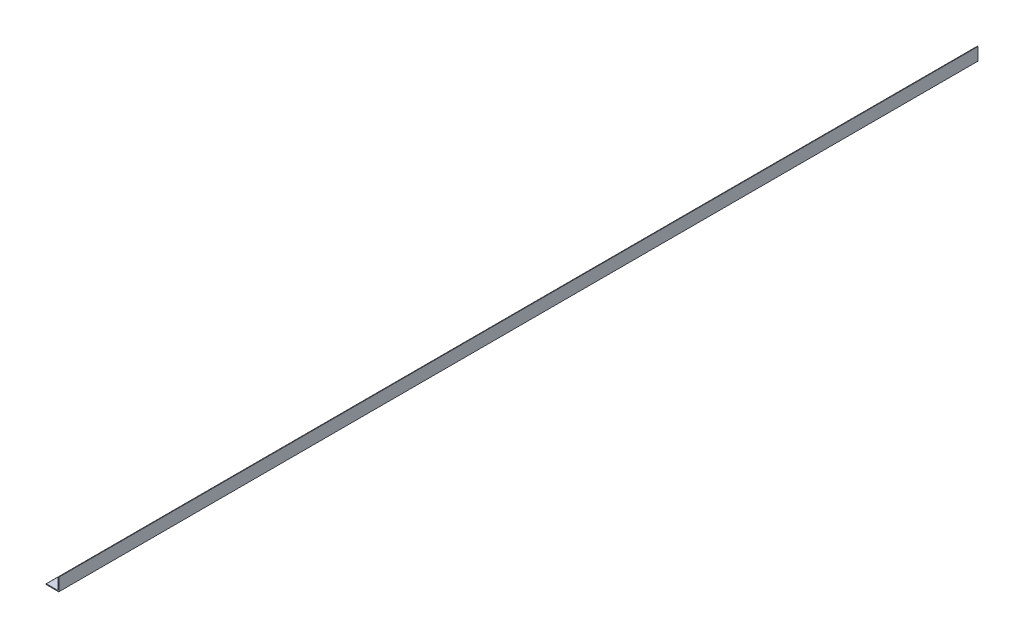
SolidWorks part; units mm, degrees
ref_plane "Front Plane" through (0, 0, 0) normal (0, 0, 1) x (1, 0, 0)
ref_plane "Top Plane" through (0, 0, 0) normal (0, 1, 0) x (1, 0, 0)
ref_plane "Right Plane" through (0, 0, 0) normal (1, 0, 0) x (0, 0, -1)
sketch "Sketch0" plane through (0, 0, 0) normal (0, 0, 1) x (1, 0, 0)
  line L0 (-12.7, -12.7) -> (12.7, -12.7)
  line L1 (12.7, -12.7) -> (12.7, 12.7)
  line L2 (12.7, 0) -> (0, 0) construction
  line L3 (0, 0) -> (0, -12.7) construction
  line L4 (11.1125, -9.5377) -> (11.1125, 12.7) construction
  line L5 (9.5377, -11.1125) -> (-12.7, -11.1125) construction
  arc A0 (11.1125, -9.5377) -> (9.5377, -11.1125) centre (9.5377, -9.5377) cw
  point P3 (10.6513, -10.6513)
  dimension "Inside Corner Radius" = 1.5748
  dimension "Outside Height" = 25.4
  dimension "Inside Height" = 23.8125
  dimension "Inside Width" = 23.8125
  dimension "Wall Thickness" = 1.5875
  dimension "D1" = 1.5875
  dimension "Outside Width" = 25.4
sketch "Sketch1" plane through (0, 0, 0) normal (1, 0, 0) x (0, 0, -1)
  line L0 (914.4, 0) -> (-914.4, 0)
  point P4 (0, 0)
  dimension "Length" = 1828.8
sketch "Sketch2" plane through (0, 0, 0) normal (0, 0, 1) x (1, 0, 0)
  line L0 (-12.7, -12.7) -> (12.7, -12.7)
  line L1 (12.7, -12.7) -> (12.7, 12.7)
  line L2 (12.7, 12.7) -> (11.1125, 12.7) construction
  line L3 (11.1125, 11.9062) -> (11.1125, -9.5377)
  line L4 (9.5377, -11.1125) -> (-11.9062, -11.1125)
  line L5 (-12.7, -12.7) -> (-12.7, -11.1125) construction
  line L6 (11.9062, 12.7) -> (12.7, 12.7)
  line L7 (-12.7, -11.9062) -> (-12.7, -12.7)
  line L8 (12.7, 0) -> (0, 0) construction
  line L9 (0, 0) -> (0, -12.7) construction
  arc A0 (11.1125, 11.9062) -> (11.9062, 12.7) centre (11.9062, 11.9062) cw
  arc A1 (-12.7, -11.9062) -> (-11.9062, -11.1125) centre (-11.9062, -11.9062) cw
  arc A2 (11.1125, -9.5377) -> (9.5377, -11.1125) centre (9.5377, -9.5377) cw
  dimension "Inside Radius" = 1.5748
  dimension "Height" = 25.4
  dimension "Width" = 25.4
  dimension "Thickness" = 1.5875
extrude "Boss-Extrude1" add sketch "Sketch2" along normal mid plane 1828.8
sketch "Break Locations" plane through (0, 0, 0) normal (1, 0, 0) x (0, 0, -1)
  line L0 (-888.492, 0) -> (888.492, 0)
  line L1 (-914.4, -12.7) -> (-914.4, 12.7) construction
  line L2 (914.4, -12.7) -> (914.4, 12.7) construction
  point P0 (-892.81, 0)
  point P1 (892.81, 0)
  point P10 (0, 0)
  point P11 (888.492, 0)
  point P13 (-888.492, 0)
  dimension "D1" = 21.59
  dimension "D2" = 21.59
  dimension "D3" = 25.908
hole_wizard "1/4-20 Tapped Hole1" positions "Sketch3" profile "Sketch4" tap size "1/4-20" standard "ANSI Inch" end condition through all
sketch "Sketch3" plane through (0, -11.1125, 0) normal (0, 1, 0) x (1, 0, 0)
  line L2 (11.1125, -914.4) -> (11.1125, 914.4) construction
  line L4 (9.5377, 914.4) -> (-11.9062, 914.4) construction
  point P0 (-1.5875, -705.104)
  point P3 (-1.5875, -705.104)
  point P11 (-1.5875, -249.428)
  point P13 (-1.5875, 661.924)
  point P15 (-1.5875, 206.248)
  dimension "D1" = 12.7
  dimension "D2" = 252.476
  dimension "D3" = 455.676
  dimension "D4" = 455.676
  dimension "D5" = 455.676
cosmetic thread "Hole Thread1" parameters "D2"=6.35
sketch "Sketch4" plane through (-1.5875, -11.1125, 705.104) normal (1, 0, 0) x (0, 0, 1)
  line L0 (0, 0) -> (0, 1.5875)
  line L1 (0, 1.5875) -> (2.5527, 1.5875)
  line L2 (2.5527, 1.5875) -> (2.5527, 0)
  line L5 (2.5527, 0) -> (0, 0)
  line L11 (0, -6.35) -> (0, 107.95) construction
  dimension "Thru Tap Drill Dia." = 5.1054
  dimension "Thru Tap Drill Depth" = 1.5875
cosmetic thread "Hole Thread2" parameters "D2"=6.35
cosmetic thread "Hole Thread3" parameters "D2"=6.35
cosmetic thread "Hole Thread4" parameters "D2"=6.35
sketch "Sketch5" plane through (0, -11.1125, 0) normal (0, 1, 0) x (1, 0, 0)
  line L0 (-1.5875, 701.675) -> (-1.5875, 720.725) construction
  line L1 (-4.6355, 701.675) -> (-4.6355, 720.725)
  line L2 (1.4605, 701.675) -> (1.4605, 720.725)
  line L3 (9.5377, 914.4) -> (-11.9062, 914.4) construction
  line L4 (11.1125, -914.4) -> (11.1125, 914.4) construction
  line L5 (-1.5875, 304.8) -> (-1.5875, 285.75) construction
  line L6 (1.4605, 304.8) -> (1.4605, 285.75)
  line L7 (-4.6355, 304.8) -> (-4.6355, 285.75)
  line L8 (-321.8956, 0) -> (278.4939, 0) construction
  line L9 (-1.5875, -336.55) -> (-1.5875, -317.5) construction
  line L10 (1.4605, -336.55) -> (1.4605, -317.5)
  line L11 (-4.6355, -336.55) -> (-4.6355, -317.5)
  line L12 (-1.5875, -717.55) -> (-1.5875, -736.6) construction
  line L13 (-4.6355, -717.55) -> (-4.6355, -736.6)
  line L14 (1.4605, -717.55) -> (1.4605, -736.6)
  line L15 (9.5377, -914.4) -> (-11.9062, -914.4) construction
  arc A0 (-4.6355, 701.675) -> (1.4605, 701.675) centre (-1.5875, 701.675) ccw
  arc A1 (1.4605, 720.725) -> (-4.6355, 720.725) centre (-1.5875, 720.725) ccw
  arc A2 (1.4605, 304.8) -> (-4.6355, 304.8) centre (-1.5875, 304.8) ccw
  arc A3 (-4.6355, 285.75) -> (1.4605, 285.75) centre (-1.5875, 285.75) ccw
  arc A4 (1.4605, -336.55) -> (-4.6355, -336.55) centre (-1.5875, -336.55) cw
  arc A5 (-4.6355, -317.5) -> (1.4605, -317.5) centre (-1.5875, -317.5) cw
  arc A6 (-4.6355, -717.55) -> (1.4605, -717.55) centre (-1.5875, -717.55) cw
  arc A7 (1.4605, -736.6) -> (-4.6355, -736.6) centre (-1.5875, -736.6) cw
  point P2 (-1.5875, 711.2)
  point P13 (-1.5875, 295.275)
  point P23 (-1.5875, -327.025)
  point P30 (-1.5875, -727.075)
  dimension "D1" = 3.048
  dimension "D5" = 3.048
  dimension "D2" = 19.05
  dimension "D3" = 203.2
  dimension "D4" = 12.7
  dimension "D6" = 19.05
  dimension "D7" = 609.6
  dimension "D8" = 317.5
  dimension "D9" = 177.8
extrude "Cut-Extrude1" cut sketch "Sketch5" against normal through all
equation "\"D1@Break Locations\" = .85 * \"Height@Sketch2\""
equation "\"D2@Break Locations\"=\"D1@Break Locations\""
equation "\"Thickness@Sketch2\"=\"wall thickness@sketch0\""
equation "\"Height@Sketch2\"=\"outside height@sketch0\""
equation "\"Width@Sketch2\"=\"outside width@sketch0\""
equation "\"Inside Radius@Sketch2\"=\"inside corner radius@sketch0\""
equation "\"Length@Boss-Extrude1\"=\"length@sketch1\""
equation "\"D3@Break Locations\"=\"D2@Break Locations\"*1.2"
equation "\"D1@Sketch0\"=\"Wall Thickness@Sketch0\""
